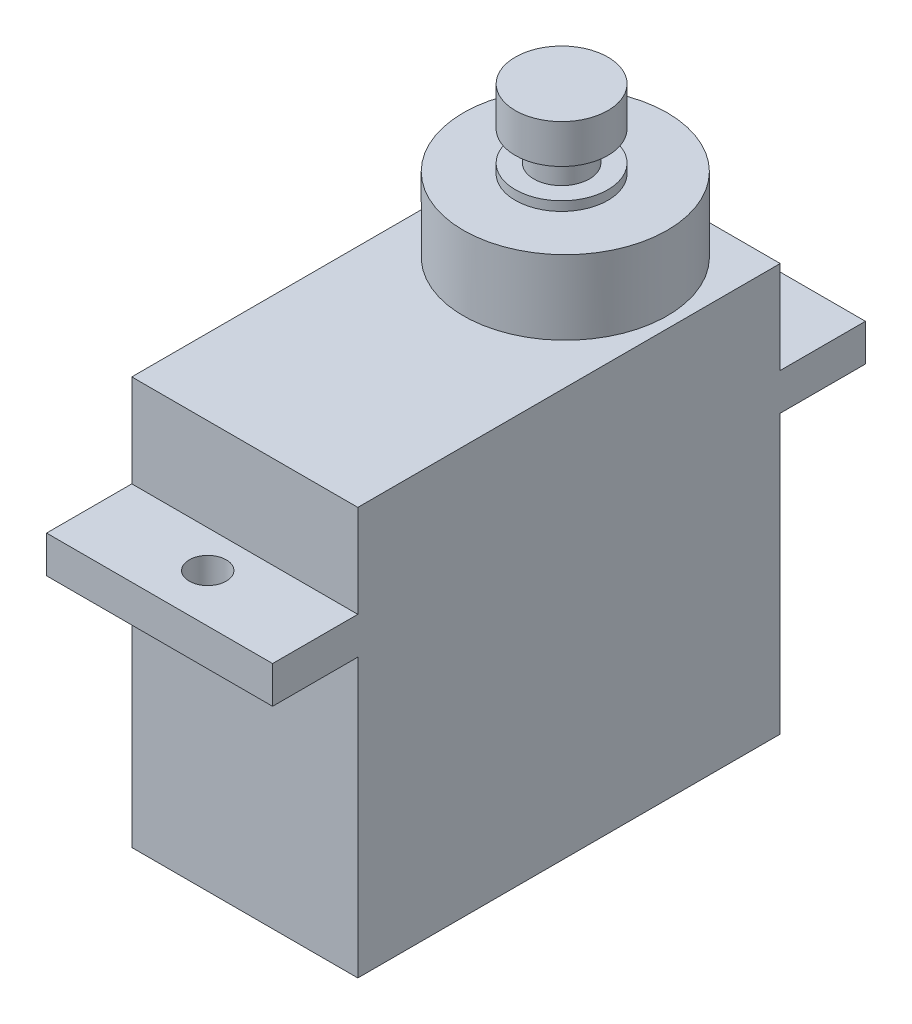
SolidWorks part; units mm, degrees
ref_plane "Front Plane" through (0, 0, 0) normal (0, 0, 1) x (1, 0, 0)
ref_plane "Top Plane" through (0, 0, 0) normal (0, 1, 0) x (1, 0, 0)
ref_plane "Right Plane" through (0, 0, 0) normal (1, 0, 0) x (0, 0, -1)
sketch "Sketch2" plane through (0, 0, 0) normal (0, 1, 0) x (1, 0, 0)
  line L1 (-6.1, -11.4) -> (6.1, -11.4)
  line L2 (-6.1, -11.4) -> (-6.1, 11.4)
  line L3 (-6.1, 11.4) -> (6.1, 11.4)
  line L4 (6.1, -11.4) -> (6.1, 11.4)
  line L5 (-6.1, -11.4) -> (6.1, 11.4) construction
  line L6 (-6.1, 11.4) -> (6.1, -11.4) construction
  point P0 (0, 0)
  dimension "D1" = 22.8
  dimension "D2" = 12.2
extrude "Boss-Extrude1" add sketch "Sketch2" along normal blind 22
ref_plane "Plane1" through (0, 15, 0) normal (0, 1, 0) x (1, 0, 0)
sketch "Sketch3" plane through (0, 15, 0) normal (0, 1, 0) x (1, 0, 0)
  line L0 (0, 11.4) -> (0, 16) construction
  line L1 (6.1, 11.4) -> (-6.1, 11.4) construction
  line L2 (-6.1, 0) -> (6.1, 0) construction
  line L3 (-6.1, 11.4) -> (-6.1, -11.4) construction
  line L4 (6.1, -11.4) -> (6.1, 11.4) construction
  line L5 (-6.1, 11.4) -> (-6.1, 16)
  line L6 (-6.1, 16) -> (6.1, 16)
  line L7 (6.1, 16) -> (6.1, 11.4)
  line L8 (-6.1, 11.4) -> (6.1, 11.4)
  line L9 (-6.1, -11.4) -> (-6.1, -16)
  line L10 (-6.1, -11.4) -> (6.1, -11.4)
  line L11 (6.1, -16) -> (6.1, -11.4)
  line L12 (-6.1, -16) -> (6.1, -16)
  line L13 (0, 11.4) -> (0, 12.4) construction
  circle A0 centre (0, 13.4) radius 1
  circle A1 centre (0, -13.4) radius 1
  dimension "D3" = 2
  dimension "D1" = 4.6
  dimension "D2" = 1
extrude "Boss-Extrude2" add sketch "Sketch3" along normal blind 2
sketch "Sketch4" plane through (0, 22, 0) normal (0, 1, 0) x (1, 0, 0)
  line L0 (0, 16) -> (0, -16) construction
  line L1 (6.1, 16) -> (-6.1, 16) construction
  line L2 (-6.1, -16) -> (6.1, -16) construction
  line L3 (-6.1, 11.4) -> (6.1, 11.4) construction
  line L4 (0, 11.4) -> (0, 5.9) construction
  circle A0 centre (0, 5.9) radius 5.5
  dimension "D1" = 5.5
  dimension "D2" = 11
extrude "Boss-Extrude3" add sketch "Sketch4" along normal blind 4
sketch "Sketch5" plane through (0, 26, 0) normal (0, 1, 0) x (1, 0, 0)
  line L0 (0, 11.4) -> (0, 0) construction
  line L1 (-6.1, 11.4) -> (6.1, 11.4) construction
  circle A0 centre (0, 5.7) radius 2.5
  dimension "D1" = 5
extrude "Boss-Extrude4" add sketch "Sketch5" along normal blind 4.2
sketch "Sketch6" plane through (0, 0, 0) normal (1, 0, 0) x (0, 0, -1)
  line L0 (7.2, 26) -> (7.2, 26.5) construction
  line L1 (11.4, 26) -> (0.4, 26) construction
  line L2 (7.2, 28.1) -> (7.2, 26.5)
  line L3 (8.2, 28.1) -> (7.2, 28.1)
  line L4 (8.2, 26) -> (8.2, 30.2) construction
  line L5 (8.2, 28.1) -> (8.2, 26.5)
  line L6 (8.2, 26.5) -> (7.2, 26.5)
  line L7 (5.7, 30.2) -> (5.7, 26) construction
  line L8 (8.2, 30.2) -> (3.2, 30.2) construction
  dimension "D1" = 1
  dimension "D2" = 0.5
revolve "Cut-Revolve1" cut sketch "Sketch6" angle 360 about L7
